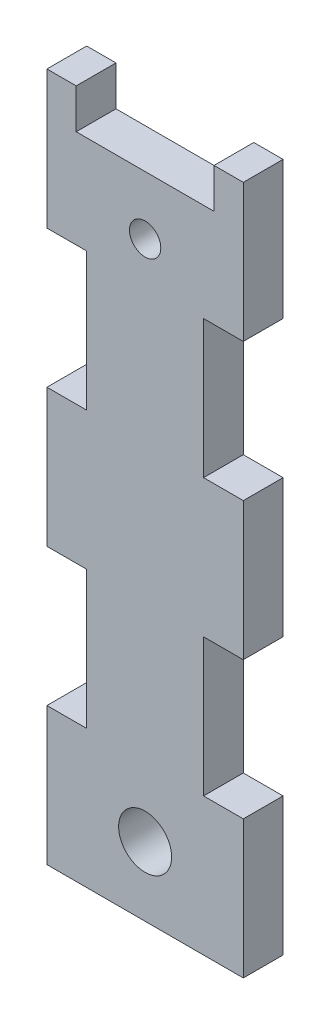
SolidWorks part; units mm, degrees
ref_plane "Front Plane" through (0, 0, 0) normal (0, 0, 1) x (1, 0, 0)
ref_plane "Top Plane" through (0, 0, 0) normal (0, 1, 0) x (1, 0, 0)
ref_plane "Right Plane" through (0, 0, 0) normal (1, 0, 0) x (0, 0, -1)
sketch "Sketch1" plane through (0, 0, 0) normal (0, 0, 1) x (1, 0, 0)
  line L0 (40.035, -9.525) -> (7.015, -9.525)
  line L1 (7.015, -9.525) -> (7.015, 0)
  line L2 (7.015, 0) -> (0, 0)
  line L3 (0, 0) -> (0, -33.02)
  line L4 (0, -33.02) -> (9.525, -33.02)
  line L5 (9.525, -33.02) -> (9.525, -66.04)
  line L6 (9.525, -66.04) -> (0, -66.04)
  line L7 (0, -66.04) -> (0, -99.06)
  line L8 (0, -99.06) -> (9.525, -99.06)
  line L9 (9.525, -99.06) -> (9.525, -132.08)
  line L10 (9.525, -132.08) -> (0, -132.08)
  line L11 (0, -132.08) -> (0, -165.1)
  line L12 (0, -165.1) -> (47.05, -165.1)
  line L13 (47.05, -165.1) -> (47.05, -132.08)
  line L14 (47.05, -132.08) -> (37.525, -132.08)
  line L15 (37.525, -132.08) -> (37.525, -99.06)
  line L16 (37.525, -99.06) -> (47.05, -99.06)
  line L17 (47.05, -99.06) -> (47.05, -66.04)
  line L18 (47.05, -66.04) -> (37.525, -66.04)
  line L19 (37.525, -66.04) -> (37.525, -33.02)
  line L20 (37.525, -33.02) -> (47.05, -33.02)
  line L21 (47.05, -33.02) -> (47.05, 0)
  line L22 (47.05, 0) -> (40.035, 0)
  line L23 (40.035, 0) -> (40.035, -9.525)
  line L24 (9.525, -9.525) -> (9.525, -37.525)
  line L25 (9.525, -37.525) -> (37.525, -37.525)
  line L26 (37.525, -37.525) -> (37.525, -9.525)
  circle A0 centre (23.525, -23.525) radius 3.75
  point P32 (23.525, -9.525)
  point P34 (37.525, -23.525)
  dimension "D6" = 7.5
  dimension "D1" = 7.015
  dimension "D2" = 9.525
  dimension "D3" = 37.525
  dimension "D4" = 28
  dimension "D5" = 28
extrude "Boss-Extrude1" add sketch "Sketch1" along normal blind 9.525 contours L24 L0 L1 L2 L3 L4 | L26 L20 L21 L22 L23 L0 | L19 L26 L0 L24 L5 L25 A0 | L25 L5 L6 L7 L8 L9 L10 L11 L12 L13 L14 L15 L16 L17 L18 L19
sketch "Sketch2" plane through (0, 0, 9.525) normal (0, 0, 1) x (1, 0, 0)
  line L0 (0, -165.1) -> (47.05, -165.1) construction
  line L1 (47.05, -165.1) -> (47.05, -132.08) construction
  circle A0 centre (23.525, -148.59) radius 6.35
  point P2 (23.525, -165.1)
  point P3 (47.05, -148.59)
  point P6 (0, 0)
  point P9 (0, 0)
  dimension "D1" = 12.7
extrude "Cut-Extrude1" cut sketch "Sketch2" against normal through all
